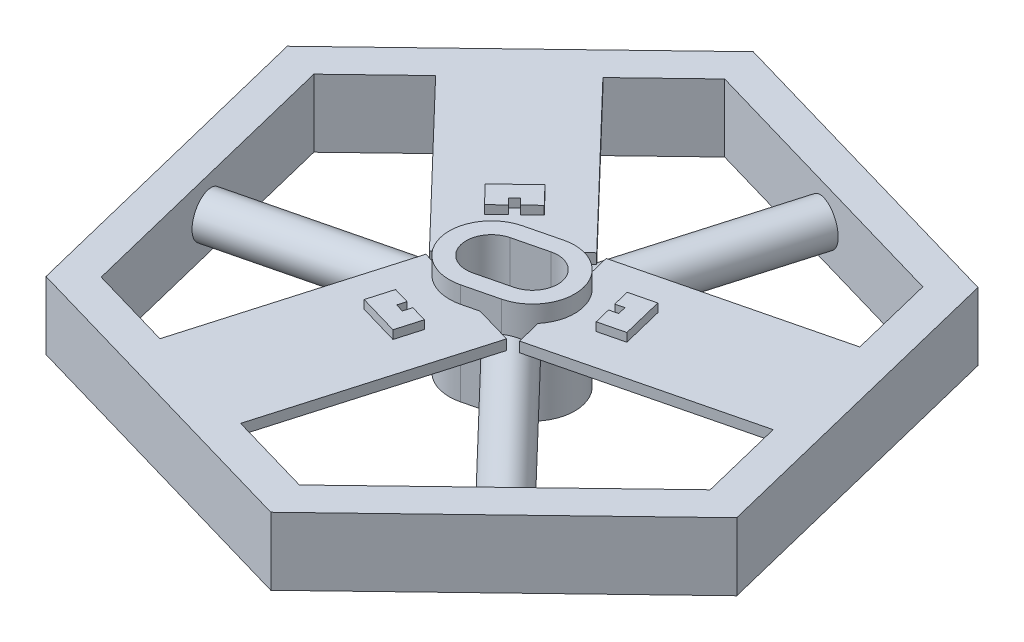
SolidWorks part; units mm, degrees
ref_plane "Front Plane" through (0, 0, 0) normal (0, 0, 1) x (1, 0, 0)
ref_plane "Top Plane" through (0, 0, 0) normal (0, 1, 0) x (1, 0, 0)
ref_plane "Right Plane" through (0, 0, 0) normal (1, 0, 0) x (0, 0, -1)
sketch "Sketch1" plane through (0, 0, 0) normal (0, 1, 0) x (1, 0, 0)
  line L0 (124.0104, 119.0508) -> (-41.0958, 166.9215)
  line L1 (187.2867, -54.3017) -> (140.6701, 135.0442)
  line L2 (140.6701, 135.0442) -> (-46.6167, 189.3459)
  line L3 (-46.6167, 189.3459) -> (-187.2867, 54.3017)
  line L4 (-187.2867, 54.3017) -> (-140.6701, -135.0442)
  line L5 (-140.6701, -135.0442) -> (46.6167, -189.3459)
  line L6 (46.6167, -189.3459) -> (187.2867, -54.3017)
  line L7 (-41.0958, 166.9215) -> (-165.1062, 47.8707)
  line L8 (-165.1062, 47.8707) -> (-124.0104, -119.0508)
  line L9 (-124.0104, -119.0508) -> (41.0958, -166.9215)
  line L10 (41.0958, -166.9215) -> (165.1062, -47.8707)
  line L11 (165.1062, -47.8707) -> (124.0104, 119.0508)
  circle A0 centre (0, 0) radius 168.875 construction
  circle A1 centre (0, 0) radius 148.875
  dimension "D1" = 195
  dimension "D2" = 20
extrude "Boss-Extrude5" add sketch "Sketch1" along normal blind 40 contours L5 L6 L1 L2 L3 L4 L11 L10 L9 L8 L7 L0
sketch "Sketch3" plane through (0, 0, 0) normal (0, -1, 0) x (1, 0, 0)
  line L0 (41.0958, 166.9215) -> (-41.0958, -166.9215) construction
  line L1 (-144.5583, 35.59) -> (144.5583, -35.59) construction
  line L2 (-165.1062, -47.8707) -> (-124.0104, 119.0508) construction
  line L3 (165.1062, 47.8707) -> (124.0104, -119.0508) construction
  line L4 (-124.0104, 119.0508) -> (124.0104, -119.0508) construction
  line L5 (-165.1062, -47.8707) -> (165.1062, 47.8707) construction
  line L6 (9.71, -2.3906) -> (-9.71, 2.3906) construction
  line L7 (6.1241, -16.9557) -> (-13.2959, -12.1745)
  line L8 (13.2959, 12.1745) -> (-6.1241, 16.9557)
  line L9 (3.7336, -26.6657) -> (-15.6865, -21.8845)
  line L10 (15.6865, 21.8845) -> (-3.7336, 26.6657)
  arc A0 (6.1241, -16.9557) -> (13.2959, 12.1745) centre (9.71, -2.3906) ccw
  arc A1 (-6.1241, 16.9557) -> (-13.2959, -12.1745) centre (-9.71, 2.3906) ccw
  arc A2 (-3.7336, 26.6657) -> (-15.6865, -21.8845) centre (-9.71, 2.3906) ccw
  arc A3 (3.7336, -26.6657) -> (15.6865, 21.8845) centre (9.71, -2.3906) ccw
  point P20 (0, 0)
  dimension "D2" = 15
  dimension "D1" = 20
  dimension "D3" = 10
extrude "Boss-Extrude9" add sketch "Sketch3" along normal blind 10 and the other way blind 50 separate body
sketch "Sketch4" plane through (-144.5583, 0, 35.59) normal (0.971, 0, -0.2391) x (-0.2391, 0, -0.971)
  line L0 (-85.953, 20) -> (85.953, 20)
  line L1 (-85.953, 40) -> (-85.953, 0) construction
  line L2 (85.953, 40) -> (85.953, 0) construction
  circle A0 centre (0, 20) radius 12.5
  dimension "D1" = 25
extrude "Boss-Extrude10" add sketch "Sketch4" along normal blind 120 contours L0 A0 | L0 A0
sketch "Sketch5" plane through (41.4573, 0, -142.9862) normal (-0.2785, 0, 0.9604) x (0.9604, 0, 0.2785)
  line L0 (-85.953, 20) -> (85.953, 20) construction
  line L1 (-85.953, 40) -> (-85.953, 0) construction
  line L2 (85.953, 40) -> (85.953, 0) construction
  circle A0 centre (0, 20) radius 12.5
  dimension "D1" = 25
extrude "Boss-Extrude11" add sketch "Sketch5" along normal blind 127
sketch "Sketch6" plane through (103.101, 0, 107.3961) normal (-0.6925, 0, -0.7214) x (-0.7214, 0, 0.6925)
  line L0 (85.953, 20) -> (-85.953, 20)
  line L1 (85.953, 40) -> (85.953, 0) construction
  line L2 (-85.953, 40) -> (-85.953, 0) construction
  circle A0 centre (0, 20) radius 12.5
  dimension "D1" = 25
extrude "Boss-Extrude12" add sketch "Sketch6" along normal blind 127 contours L0 A0 | L0 A0
sketch "Sketch8" plane through (-103.101, 0, -107.3961) normal (0.6925, 0, 0.7214) x (0.7214, 0, -0.6925)
  line L0 (0, 37) -> (0, 0) construction
  line L1 (85.953, 0) -> (-85.953, 0) construction
  line L2 (85.953, 40) -> (-85.953, 40) construction
  line L3 (-35, 34) -> (35, 34)
  line L4 (-35, 34) -> (-35, 40)
  line L5 (-35, 40) -> (35, 40)
  line L6 (35, 34) -> (35, 40)
  line L7 (-35, 34) -> (35, 40) construction
  line L8 (-35, 40) -> (35, 34) construction
  point P4 (0, 37)
  dimension "D1" = 70
  dimension "D2" = 6
extrude "Boss-Extrude14" add sketch "Sketch8" along normal blind 127
sketch "Sketch9" plane through (-41.4573, 0, 142.9862) normal (0.2785, 0, -0.9604) x (-0.9604, 0, -0.2785)
  line L0 (0, 40) -> (0, 0) construction
  line L1 (85.953, 40) -> (-85.953, 40) construction
  line L2 (85.953, 0) -> (-85.953, 0) construction
  line L4 (-35, 34) -> (35, 34)
  line L5 (-35, 34) -> (-35, 40)
  line L6 (-35, 40) -> (35, 40)
  line L7 (35, 34) -> (35, 40)
  line L8 (-35, 34) -> (35, 40) construction
  line L9 (-35, 40) -> (35, 34) construction
  point P6 (0, 37)
  dimension "D1" = 70
  dimension "D2" = 6
extrude "Boss-Extrude15" add sketch "Sketch9" along normal blind 127
sketch "Sketch10" plane through (144.5583, 0, -35.59) normal (-0.971, 0, 0.2391) x (0.2391, 0, 0.971)
  line L0 (0, 0) -> (0, 40) construction
  line L1 (85.953, 0) -> (-85.953, 0) construction
  line L2 (85.953, 40) -> (-85.953, 40) construction
  line L4 (-35, 34) -> (35, 34)
  line L5 (-35, 34) -> (-35, 40)
  line L6 (-35, 40) -> (35, 40)
  line L7 (35, 34) -> (35, 40)
  line L8 (-35, 34) -> (35, 40) construction
  line L9 (-35, 40) -> (35, 34) construction
  point P6 (0, 37)
  dimension "D1" = 6
  dimension "D2" = 70
extrude "Boss-Extrude16" add sketch "Sketch10" along normal blind 124
sketch "Sketch13" plane through (0, 40, 0) normal (0, 1, 0) x (1, 0, 0)
  line L0 (92.7231, -13.2169) -> (75.9889, 54.7535)
  line L1 (32.5208, -28.0386) -> (152.9254, 1.6049) construction
  line L2 (15.7866, 39.9318) -> (136.1912, 69.5752) construction
sketch "Sketch14" plane through (0, 40, 0) normal (0, 1, 0) x (1, 0, 0)
  line L0 (20.0453, -56.5502) -> (-47.1858, -37.0573) construction
  line L1 (27.524, -30.7562) -> (-7.8417, -152.7326) construction
  line L2 (-39.7071, -11.2632) -> (-75.0728, -133.2397) construction
  line L3 (-58.9966, 10.9153) -> (-8.4996, 59.3927) construction
  line L4 (38.9512, 45.6349) -> (55.6854, -22.3355) construction
  line L5 (47.3183, 11.6497) -> (60.3575, 14.8599) construction
  line L6 (50.3066, -0.4879) -> (64.8717, 3.098)
  line L7 (64.8717, 3.098) -> (58.8952, 27.3732)
  line L8 (44.3301, 23.7873) -> (58.8952, 27.3732)
  line L9 (-25.5758, -43.3229) -> (-29.7529, -57.7295)
  line L10 (-29.7529, -57.7295) -> (-5.7417, -64.6913)
  line L11 (-1.5647, -50.2846) -> (-5.7417, -64.6913)
  line L12 (-24.7308, 43.8107) -> (-35.1188, 54.6315)
  line L13 (-35.1188, 54.6315) -> (-53.1534, 37.3181)
  line L14 (-42.7654, 26.4974) -> (-53.1534, 37.3181)
  point P12 (0, 0)
  point P18 (61.8834, 15.2356)
  point P29 (0, 0)
  dimension "D2" = 25
  dimension "D3" = 15
  dimension "D1" = 3
  dimension "D4" = 3
extrude "Extrude-Thin1" add sketch "Sketch14" along normal blind 5 thin thin type one direction wall 10
